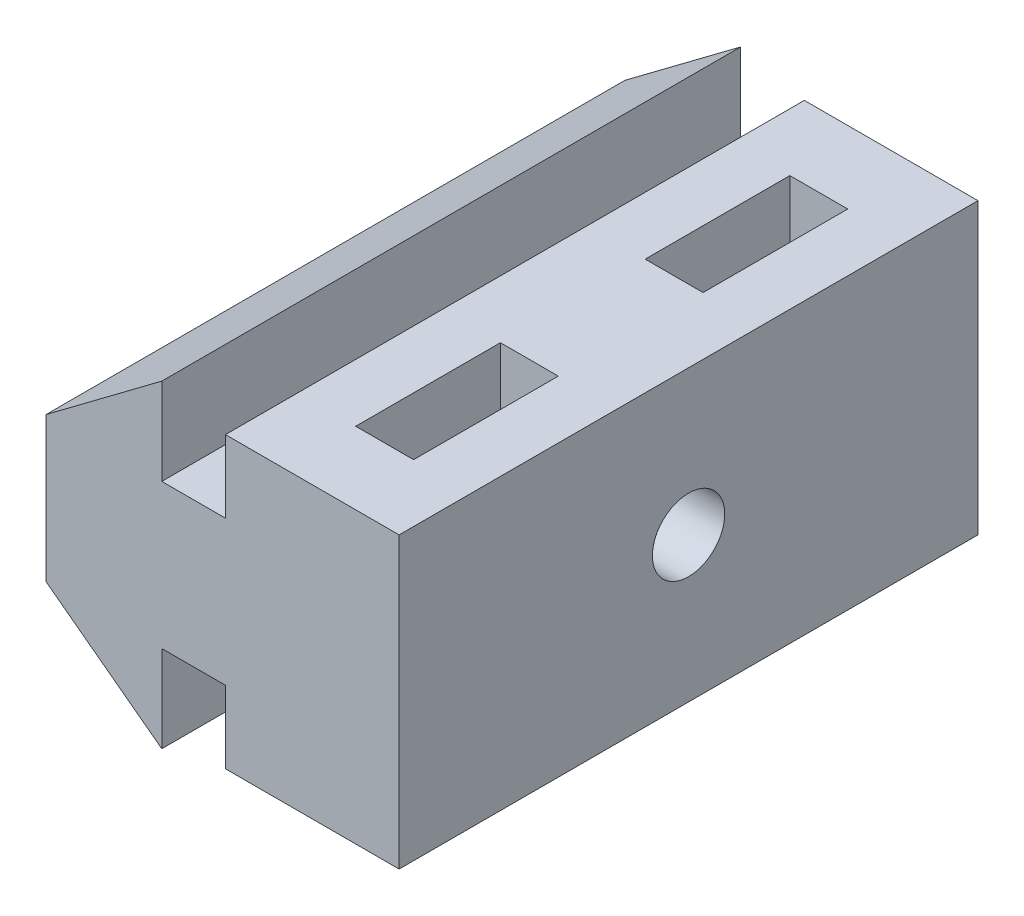
SolidWorks part; units mm, degrees
ref_plane "Plan de face" through (0, 0, 0) normal (0, 0, 1) x (1, 0, 0)
ref_plane "Plan de dessus" through (0, 0, 0) normal (0, 1, 0) x (1, 0, 0)
ref_plane "Plan de droite" through (0, 0, 0) normal (1, 0, 0) x (0, 0, -1)
sketch "ProfileRainureEsquisse" plane through (0, 0, 0) normal (0, 0, 1) x (1, 0, 0)
  line L0 (0, 0) -> (0, 5)
  line L1 (0, 5) -> (4, 8)
  line L2 (0, 0) -> (4, -3)
  line L3 (4, 8) -> (4, 5)
  line L4 (4, 5) -> (6.2, 5)
  line L5 (6.2, 0) -> (6.2, -2.5)
  line L6 (6.2, 0) -> (4, 0)
  line L7 (4, 0) -> (4, -3)
  line L8 (6.2, 5) -> (6.2, 7.5)
  line L9 (6.2, 7.5) -> (12.2, 7.5)
  line L10 (6.2, -2.5) -> (12.2, -2.5)
  line L11 (12.2, -2.5) -> (12.2, 7.5)
  point P4 (0, 2.5)
  point P14 (12.2, 2.5)
  dimension "D1" = 4
  dimension "D2" = 2.2
  dimension "D3" = 5
  dimension "D4" = 8
  dimension "D5" = 6
  dimension "D6" = 10
extrude "Boss.-Extru.1" add sketch "ProfileRainureEsquisse" along normal blind 20
sketch "Esquisse1" plane through (12.2, 0, 0) normal (1, 0, 0) x (0, 0, -1)
  line L0 (-20, 7.5) -> (0, 7.5) construction
  line L1 (-20, -2.5) -> (-20, 7.5) construction
  circle A0 centre (-10, 2.5) radius 1.25
  point P2 (-10, 7.5)
  point P3 (-20, 2.5)
  dimension "D1" = 2.5
extrude "Enlèv. mat.-Extru.1" cut sketch "Esquisse1" against normal through all
sketch "Esquisse2" plane through (0, 7.5, 0) normal (0, 1, 0) x (1, 0, 0)
  line L0 (12.2, 0) -> (6.2, 0) construction
  line L1 (12.2, -20) -> (6.2, -20) construction
  line L2 (6.2, -20) -> (6.2, 0) construction
  line L3 (8.2, -12.5) -> (10.2, -12.5)
  line L4 (8.2, -12.5) -> (8.2, -17.5)
  line L5 (8.2, -17.5) -> (10.2, -17.5)
  line L6 (10.2, -12.5) -> (10.2, -17.5)
  line L8 (8.2, -2.5) -> (10.2, -2.5)
  line L9 (8.2, -2.5) -> (8.2, -7.5)
  line L10 (8.2, -7.5) -> (10.2, -7.5)
  line L11 (10.2, -2.5) -> (10.2, -7.5)
  point P2 (9.2, 0)
  dimension "D1" = 5
  dimension "D3" = 2.5
  dimension "D2" = 2
  dimension "D4" = 2
  dimension "D5" = 2.5
extrude "Enlèv. mat.-Extru.2" cut sketch "Esquisse2" against normal through all
